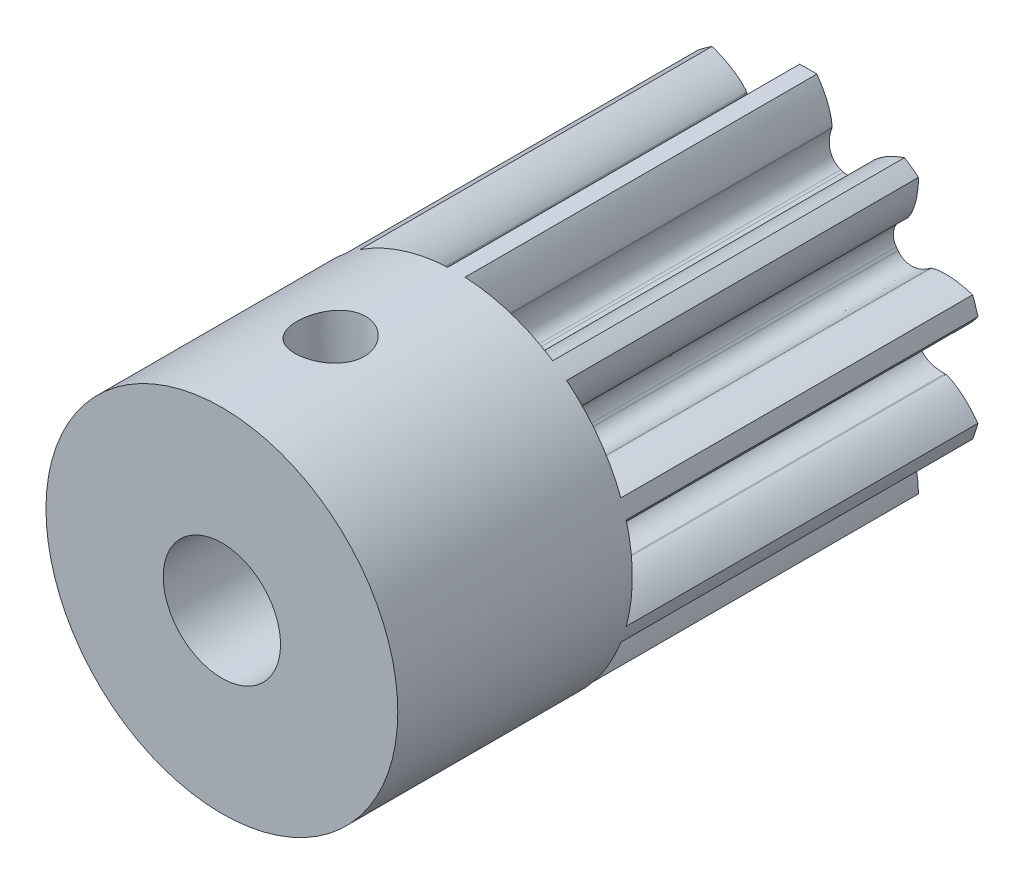
SolidWorks part; units mm, degrees
ref_plane "Front Plane" through (0, 0, 0) normal (0, 0, 1) x (1, 0, 0)
ref_plane "Top Plane" through (0, 0, 0) normal (0, 1, 0) x (1, 0, 0)
ref_plane "Right Plane" through (0, 0, 0) normal (1, 0, 0) x (0, 0, -1)
sketch "Pitch Diameter" plane through (0, 0, 0) normal (0, 0, 1) x (1, 0, 0)
  circle A0 centre (0, 0) radius 2.5
  dimension "D1" = 5
sketch "Sketch1" plane through (0, 0, 0) normal (0, 0, 1) x (1, 0, 0)
  line L0 (0.4038, 2.337) -> (0.4008, 2.3209)
  line L1 (0, 3.1774) -> (0, 0) construction
  line L2 (0, 0) -> (0, 3.1774) construction
  line L3 (-0.4038, 2.337) -> (-0.4008, 2.3209)
  arc A0 (-0.5564, 1.7905) -> (0.5564, 1.7905) centre (0, 0) ccw
  spline S0 degree 3 poles (0, 3.1774) (0.0678, 3.1029) (0.1575, 2.9894) (0.2528, 2.8331) (0.3056, 2.7295) (0.3448, 2.6351) (0.3723, 2.5513) (0.39, 2.4792) (0.4015, 2.4093) (0.4046, 2.3631) (0.4038, 2.337) knots 0 0 0 0 0.317754 0.454552 0.576631 0.68399 0.776631 0.854552 0.917754 1 1 1 1
  spline S1 degree 3 poles (0.4008, 2.3209) (0.3867, 2.2821) (0.3701, 2.2234) (0.3595, 2.1443) (0.3579, 2.087) (0.3631, 2.0303) (0.3766, 1.9738) (0.4004, 1.9179) (0.4514, 1.8443) (0.5107, 1.8045) (0.5564, 1.7905) knots 0 0 0 0 0.200126 0.294348 0.386168 0.477231 0.569745 0.66645 0.770113 1 1 1 1
  spline S2 degree 3 poles (-0.4008, 2.3209) (-0.3867, 2.2821) (-0.3701, 2.2234) (-0.3595, 2.1443) (-0.3579, 2.087) (-0.3631, 2.0303) (-0.3766, 1.9738) (-0.4004, 1.9179) (-0.4514, 1.8443) (-0.5107, 1.8045) (-0.5564, 1.7905) knots 0 0 0 0 0.200126 0.294348 0.386168 0.477231 0.569745 0.66645 0.770113 1 1 1 1
  spline S3 degree 3 poles (0, 3.1774) (-0.0678, 3.1029) (-0.1575, 2.9894) (-0.2528, 2.8331) (-0.3056, 2.7295) (-0.3448, 2.6351) (-0.3723, 2.5513) (-0.39, 2.4792) (-0.4015, 2.4093) (-0.4046, 2.3631) (-0.4038, 2.337) knots 0 0 0 0 0.317754 0.454552 0.576631 0.68399 0.776631 0.854552 0.917754 1 1 1 1
  point P2 (0, 3.1774)
  point P4 (0.102, 3.0565)
  point P5 (0.1861, 2.9395)
  point P6 (0.2537, 2.8283)
  point P7 (0.3062, 2.7247)
  point P8 (0.3453, 2.6303)
  point P9 (0.3726, 2.5465)
  point P10 (0.3901, 2.4745)
  point P11 (0.3997, 2.4151)
  point P12 (0.4036, 2.3691)
  point P13 (0.4038, 2.337)
  point P14 (0.4008, 2.3209)
  point P15 (0.3815, 2.2606)
  point P18 (0.368, 2.2016)
  point P19 (0.3604, 2.1437)
  point P20 (0.359, 2.0869)
  point P21 (0.3644, 2.0308)
  point P22 (0.3779, 1.9751)
  point P23 (0.4016, 1.9202)
  point P24 (0.4383, 1.8676)
  point P25 (0.4905, 1.822)
  point P26 (0.5564, 1.7905)
other "AlignGroup4" parameters "D1"=14.359, "D2"=4.3343, "D3"=15.4996, "D4"=22.2419, "D5"=0.2537, "D6"=0.3062, "D7"=0.3453, "D8"=0.3726, "D9"=0.3901, "D10"=0.3997, "D11"=0.4036, "D12"=0.4038, "D13"=0.4008, "D14"=0.3815, "D15"=0.368, "D16"=0.3604, "D17"=0.359, "D18"=0.3644, "D19"=0.3779, "D20"=0.4016, "D21"=0.4383, "D22"=0.4905, "D23"=0.5564, "D24"=0, "D25"=3.1774, "D26"=3.0565, "D27"=2.9395, "D28"=2.8283, "D29"=2.7247, "D30"=2.6303, "D31"=2.5465, "D32"=2.4745, "D33"=2.4151, "D34"=2.3691, "D35"=2.337, "D36"=2.3209, "D37"=2.2606, "D38"=2.2016, "D39"=2.1437, "D40"=2.0869, "D41"=2.0308, "D42"=1.9751, "D43"=1.9202, "D44"=1.8676, "D45"=1.822, "D46"=1.7905
other "AlignGroup5"
extrude "Tooth" add sketch "Sketch1" along normal blind 5 and the other way blind 1
pattern_circular "Teeth" count 10 over 360 about axis through (0, 0, -1) along (0, 0, 1) of "Tooth"
sketch "Sketch6" plane through (0, 0, 0) normal (0, 0, 1) x (1, 0, 0)
  circle A0 centre (0, 0) radius 3
  dimension "D1" = 6
extrude "Addendum" cut sketch "Sketch6" along normal through all both and the other way through all flip side to cut
sketch "Sketch9" plane through (0, 0, 5) normal (0, 0, 1) x (1, 0, 0)
  circle A0 centre (0, 0) radius 3
extrude "Boss-Extrude1" add sketch "Sketch9" along normal blind 4
ref_plane "Plane1" through (0.1469, -2.9964, 0) normal (0.049, -0.9988, 0) x (-0.9988, -0.049, 0)
sketch "Sketch11" plane through (0, 0, -1) normal (0, 0, -1) x (-1, 0, 0)
  circle A0 centre (0, 0) radius 1
sketch "Sketch12" plane through (0.1469, -2.9964, 0) normal (0.049, -0.9988, 0) x (-0.9988, -0.049, 0)
  line L0 (0, -5) -> (0, -9) construction
  line L1 (-3, -9) -> (3, -9) construction
  circle A0 centre (0, -7) radius 0.575
extrude "Cut-Extrude1" cut sketch "Sketch11" against normal through all
extrude "Cut-Extrude2" cut sketch "Sketch12" against normal through all
